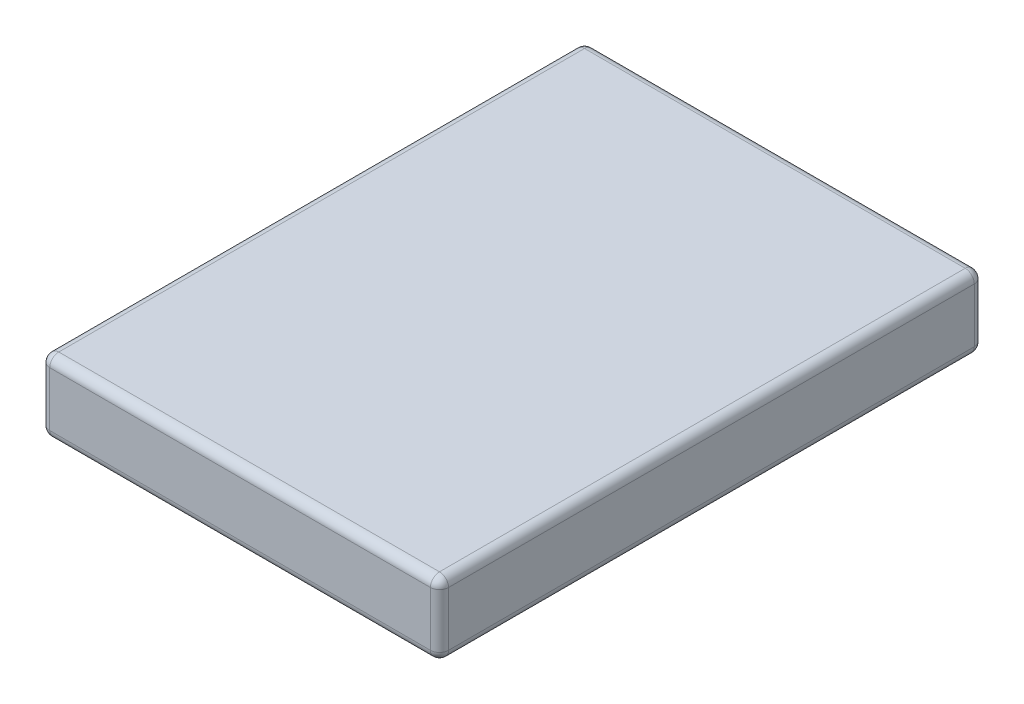
SolidWorks part; units mm, degrees
ref_plane "Plan de face" through (0, 0, 0) normal (0, 0, 1) x (1, 0, 0)
ref_plane "Plan de dessus" through (0, 0, 0) normal (0, 1, 0) x (1, 0, 0)
ref_plane "Plan de droite" through (0, 0, 0) normal (1, 0, 0) x (0, 0, -1)
sketch "Esquisse1" plane through (0, 0, 0) normal (0, 1, 0) x (1, 0, 0)
  line L1 (5.5, -7.5) -> (-5.5, -7.5)
  line L2 (5.5, -7.5) -> (5.5, 7.5)
  line L3 (5.5, 7.5) -> (-5.5, 7.5)
  line L4 (-5.5, -7.5) -> (-5.5, 7.5)
  line L5 (5.5, -7.5) -> (-5.5, 7.5) construction
  line L6 (5.5, 7.5) -> (-5.5, -7.5) construction
  point P0 (0, 0)
  dimension "D1" = 15
  dimension "D2" = 11
extrude "Boss.-Extru.1" add sketch "Esquisse1" along normal blind 2
fillet "Congé1" radius 0.25 12 edges at (-5.5, 1, -7.5) (0, 0, -7.5) (-5.5, 0, 0) (5.5, 1, -7.5) (5.5, 0, 0) (0, 2, -7.5) (5.5, 2, 0) (-5.5, 2, 0) (-5.5, 1, 7.5) (0, 2, 7.5) (5.5, 1, 7.5) (0, 0, 7.5)
